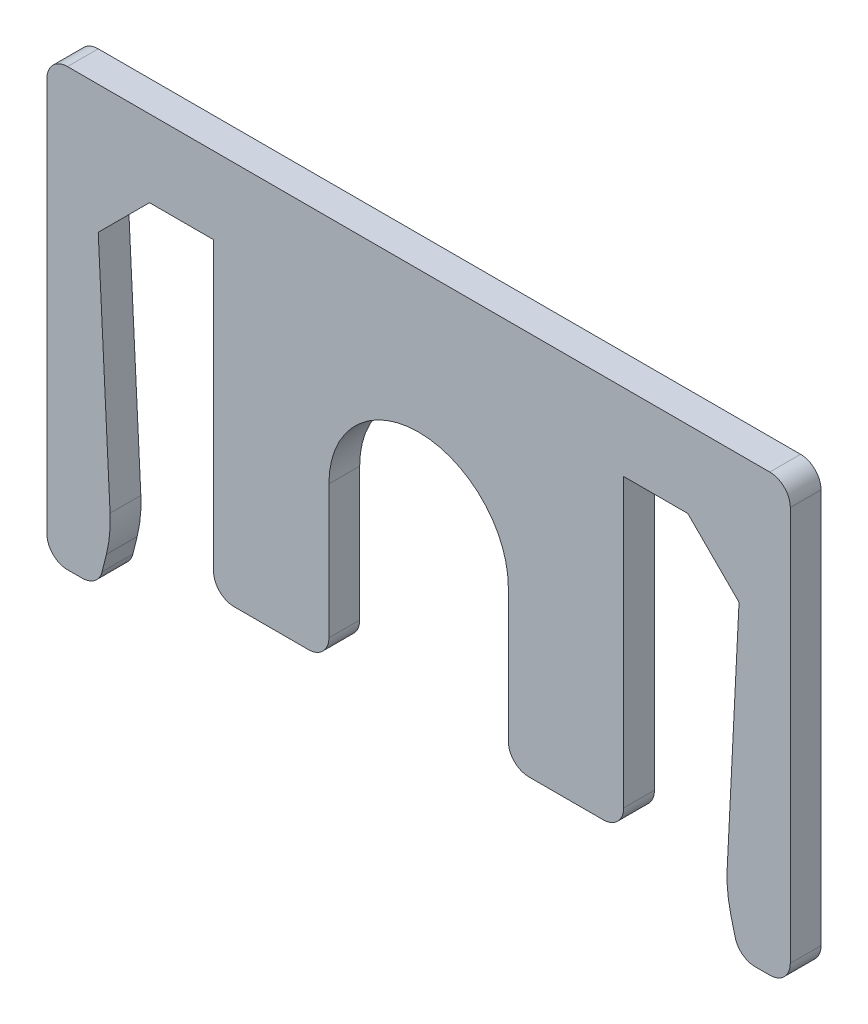
SolidWorks part; units mm, degrees
ref_plane "Front Plane" through (0, 0, 0) normal (0, 0, 1) x (1, 0, 0)
ref_plane "Top Plane" through (0, 0, 0) normal (0, 1, 0) x (1, 0, 0)
ref_plane "Right Plane" through (0, 0, 0) normal (1, 0, 0) x (0, 0, -1)
sketch "Sketch1" plane through (0, 0, 0) normal (0, 0, 1) x (1, 0, 0)
  line L0 (-12.5, 0) -> (-10.5, 0) construction
  line L1 (-10.5, 0) -> (-12.5, -2)
  line L2 (-12.5, -2) -> (-12.5, 0) construction
  line L3 (12.5, 0) -> (12.5, -2) construction
  line L4 (12.5, -2) -> (10.5, 0)
  line L5 (10.5, 0) -> (12.5, 0) construction
  line L6 (-12.5, -2) -> (-12, -12)
  line L7 (-12, -12) -> (-12.5, -14)
  line L8 (-12.5, -14) -> (-12.5, -2) construction
  line L9 (12.5, -2) -> (12.5, -14) construction
  line L10 (12.5, -14) -> (12, -12)
  line L11 (12, -12) -> (12.5, -2)
  line L12 (-10.5, 0) -> (-8, 0) construction
  line L13 (-3.5, -12) -> (3.5, -12) construction
  line L14 (-12.5, -14) -> (-14.5, -14)
  line L15 (-12.5, -14) -> (-12.5, -2) construction
  line L16 (-12.5, 3) -> (-14.5, 3)
  line L17 (-14.5, -14) -> (-14.5, 3)
  line L18 (12.5, -14) -> (14.5, -14)
  line L19 (12.5, -14) -> (12.5, -2) construction
  line L20 (12.5, 3) -> (14.5, 3)
  line L21 (14.5, -14) -> (14.5, 3)
  line L22 (-12.5, 3) -> (12.5, 3)
  line L23 (-12.5, 3) -> (-12.5, 0) construction
  line L24 (-10.5, 0) -> (-8, 0)
  line L25 (12.5, 3) -> (12.5, 0) construction
  line L26 (-3.5, -6) -> (3.5, -6) construction
  line L27 (-3.5, -6) -> (-3.5, -12)
  line L28 (-3.5, -12) -> (3.5, -12) construction
  line L29 (3.5, -6) -> (3.5, -12)
  line L30 (-8, -12) -> (-3.5, -12)
  line L31 (-8, -12) -> (-8, 0)
  line L32 (-8, 0) -> (8, 0) construction
  line L33 (8, -12) -> (8, 0)
  line L34 (-4.5, -3) -> (4.5, -3) construction
  line L35 (-4.5, -3) -> (-4.5, -12) construction
  line L36 (-4.5, -12) -> (-3.5, -12) construction
  line L37 (4.5, -3) -> (4.5, -12) construction
  line L38 (-4.5, -3) -> (4.5, -12) construction
  line L39 (-4.5, -12) -> (4.5, -3) construction
  line L40 (3.5, -12) -> (8, -12)
  line L41 (-3.5, -12) -> (3.5, -12) construction
  line L42 (3.5, -12) -> (4.5, -12) construction
  line L43 (-8, 0) -> (8, 0) construction
  line L44 (8, 0) -> (10.5, 0) construction
  line L45 (-8, 0) -> (8, 0) construction
  line L46 (8, 0) -> (10.5, 0)
  line L47 (-12.5, -2) -> (-12.5, 0) construction
  line L48 (-12.5, 0) -> (-12.5, 3) construction
  line L49 (-12.5, 0) -> (-10.5, 0) construction
  line L50 (12.5, 0) -> (12.5, 3) construction
  line L51 (10.5, 0) -> (12.5, 0) construction
  line L52 (12.5, -2) -> (12.5, 0) construction
  arc A0 (3.5, -6) -> (-3.5, -6) centre (0, -6) ccw
  arc A1 (-3.5, -6) -> (-1.6085, -9.1085) centre (0, -6) ccw construction
  arc A2 (-1.6085, -9.1085) -> (1.6085, -9.1085) centre (0, -6) ccw construction
  arc A3 (1.6085, -9.1085) -> (3.5, -6) centre (0, -6) ccw construction
  point P28 (0, 0)
  point P29 (0, -7.5)
  point P34 (5.8042, -3.4177)
  point P35 (-0.1925, -6.6497)
  point P37 (0, -6.898)
  point P38 (0, -7.5)
  point P39 (0, 0)
  point P40 (0, -7.5)
  point P41 (0, -5.5852)
  dimension "D12" = 7
  dimension "D1" = 2
  dimension "D2" = 2
  dimension "D3" = 2
  dimension "D4" = 0.5
  dimension "D5" = 2
  dimension "D6" = 10
  dimension "D7" = 0.5
  dimension "D8" = 21
  dimension "D9" = 2
  dimension "D10" = 2
  dimension "D11" = 3
  dimension "D13" = 16
  dimension "D14" = 9
  dimension "D15" = 9
  dimension "D16" = 10.5
  dimension "D17" = 1.5
extrude "Boss-Extrude1" add sketch "Sketch1" along normal blind 1.2
fillet "Fillet1" radius 5 2 edges at (-12, -12, 0.6) (12, -12, 0.6)
fillet "Fillet2" radius 0.8 10 edges at (14.5, 3, 0.6) (-14.5, 3, 0.6) (14.5, -14, 0.6) (-14.5, -14, 0.6) (12.5, -14, 0.6) (-12.5, -14, 0.6) (-8, -12, 0.6) (8, -12, 0.6) (3.5, -12, 0.6) (-3.5, -12, 0.6)
